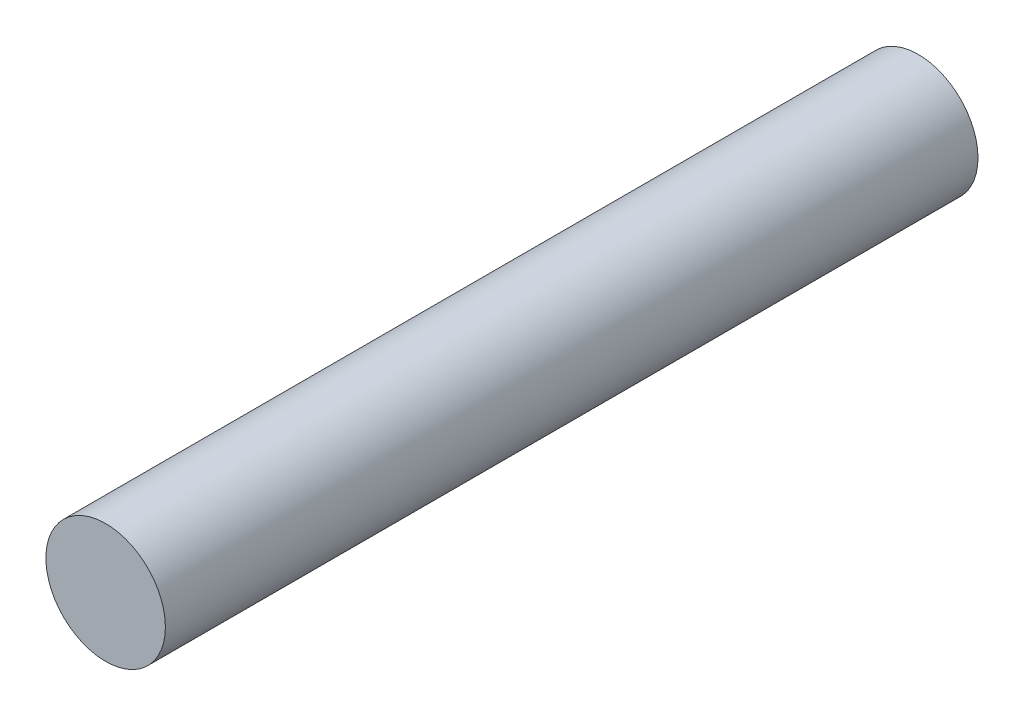
SolidWorks part; units mm, degrees
ref_plane "Front Plane" through (0, 0, 0) normal (0, 0, 1) x (1, 0, 0)
ref_plane "Top Plane" through (0, 0, 0) normal (0, 1, 0) x (1, 0, 0)
ref_plane "Right Plane" through (0, 0, 0) normal (1, 0, 0) x (0, 0, -1)
sketch "Sketch1" plane through (0, 0, 0) normal (0, 0, 1) x (1, 0, 0)
  circle A0 centre (0, 0) radius 2.5
  dimension "D1" = 5
extrude "Boss-Extrude1" add sketch "Sketch1" along normal blind 34
